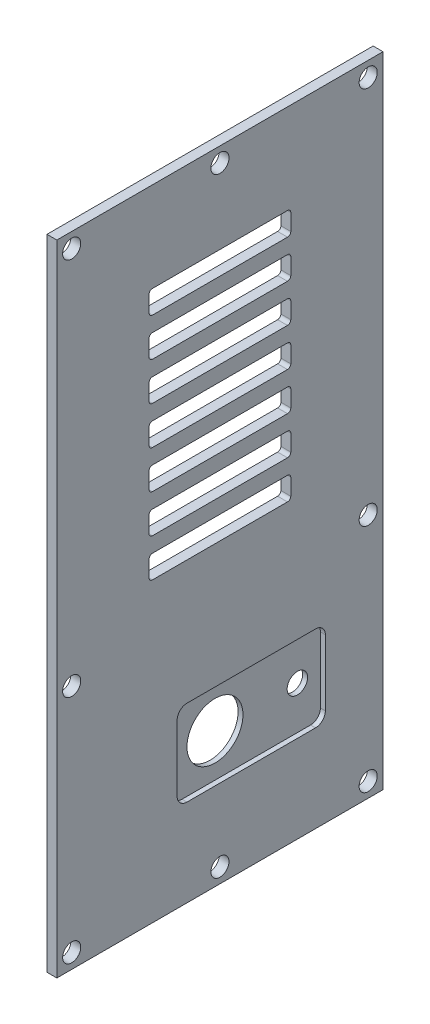
SolidWorks part; units mm, degrees
ref_plane "Front Plane" through (0, 0, 0) normal (0, 0, 1) x (1, 0, 0)
ref_plane "Top Plane" through (0, 0, 0) normal (0, 1, 0) x (1, 0, 0)
ref_plane "Right Plane" through (0, 0, 0) normal (1, 0, 0) x (0, 0, -1)
sketch "Sketch1" plane through (-74.9883, 0, 0) normal (-1, 0, 0) x (0, 0, 1)
  line L0 (-65.7307, 104.5) -> (-65.7307, -89.5)
  line L1 (-66.2307, 105) -> (33.7693, 105) construction
  line L2 (-66.2307, 105) -> (-66.2307, -90) construction
  line L3 (-66.2307, -90) -> (33.7693, -90) construction
  line L4 (33.7693, 105) -> (33.7693, -90) construction
  line L5 (-65.7307, -89.5) -> (33.2693, -89.5)
  line L6 (33.2693, 104.5) -> (33.2693, -89.5)
  line L7 (-65.7307, 104.5) -> (33.2693, 104.5)
  dimension "D1" = 0.5
extrude "Boss-Extrude1" add sketch "Sketch1" along normal blind 3
sketch "Sketch2" plane through (-77.9883, 0, 0) normal (-1, 0, 0) x (0, 0, 1)
  line L0 (-65.7307, 73.75) -> (33.2693, 73.75) construction
  line L1 (-65.7307, 104.5) -> (-65.7307, -89.5) construction
  line L2 (33.2693, -89.5) -> (33.2693, 104.5) construction
  line L3 (-16.2307, 104.5) -> (-16.2307, -89.5) construction
  line L4 (33.2693, 104.5) -> (-65.7307, 104.5) construction
  line L5 (-65.7307, -89.5) -> (33.2693, -89.5) construction
  line L6 (-65.7307, 62.15) -> (33.2693, 62.15) construction
  line L7 (33.2693, 50.55) -> (-65.7307, 50.55) construction
  line L8 (33.2693, 38.95) -> (-65.7307, 38.95) construction
  line L9 (-65.7307, 27.35) -> (33.2693, 27.35) construction
  line L10 (33.2693, 15.75) -> (-65.7307, 15.75) construction
  line L11 (33.2693, 4.15) -> (-65.7307, 4.15) construction
  line L13 (-37.7307, 70.25) -> (5.2693, 70.25)
  line L14 (-37.7307, 70.25) -> (-37.7307, 77.25)
  line L15 (-37.7307, 77.25) -> (5.2693, 77.25)
  line L16 (5.2693, 70.25) -> (5.2693, 77.25)
  line L17 (-37.7307, 70.25) -> (5.2693, 77.25) construction
  line L18 (-37.7307, 77.25) -> (5.2693, 70.25) construction
  line L19 (-37.7307, 58.65) -> (5.2693, 58.65)
  line L20 (-37.7307, 58.65) -> (-37.7307, 65.65)
  line L21 (-37.7307, 65.65) -> (5.2693, 65.65)
  line L22 (5.2693, 58.65) -> (5.2693, 65.65)
  line L23 (-37.7307, 58.65) -> (5.2693, 65.65) construction
  line L24 (-37.7307, 65.65) -> (5.2693, 58.65) construction
  line L25 (-37.7307, 47.05) -> (5.2693, 47.05)
  line L26 (-37.7307, 47.05) -> (-37.7307, 54.05)
  line L27 (-37.7307, 54.05) -> (5.2693, 54.05)
  line L28 (5.2693, 47.05) -> (5.2693, 54.05)
  line L29 (-37.7307, 47.05) -> (5.2693, 54.05) construction
  line L30 (-37.7307, 54.05) -> (5.2693, 47.05) construction
  line L31 (-37.7307, 35.45) -> (5.2693, 35.45)
  line L32 (-37.7307, 35.45) -> (-37.7307, 42.45)
  line L33 (-37.7307, 42.45) -> (5.2693, 42.45)
  line L34 (5.2693, 35.45) -> (5.2693, 42.45)
  line L35 (-37.7307, 35.45) -> (5.2693, 42.45) construction
  line L36 (-37.7307, 42.45) -> (5.2693, 35.45) construction
  line L37 (-37.7307, 23.85) -> (5.2693, 23.85)
  line L38 (-37.7307, 23.85) -> (-37.7307, 30.85)
  line L39 (-37.7307, 30.85) -> (5.2693, 30.85)
  line L40 (5.2693, 23.85) -> (5.2693, 30.85)
  line L41 (-37.7307, 23.85) -> (5.2693, 30.85) construction
  line L42 (-37.7307, 30.85) -> (5.2693, 23.85) construction
  line L43 (-37.7307, 12.25) -> (5.2693, 12.25)
  line L44 (-37.7307, 12.25) -> (-37.7307, 19.25)
  line L45 (-37.7307, 19.25) -> (5.2693, 19.25)
  line L46 (5.2693, 12.25) -> (5.2693, 19.25)
  line L47 (-37.7307, 12.25) -> (5.2693, 19.25) construction
  line L48 (-37.7307, 19.25) -> (5.2693, 12.25) construction
  line L49 (-37.7307, 0.65) -> (5.2693, 0.65)
  line L50 (-37.7307, 0.65) -> (-37.7307, 7.65)
  line L51 (-37.7307, 7.65) -> (5.2693, 7.65)
  line L52 (5.2693, 0.65) -> (5.2693, 7.65)
  line L53 (-37.7307, 0.65) -> (5.2693, 7.65) construction
  line L54 (-37.7307, 7.65) -> (5.2693, 0.65) construction
  point P24 (-16.2307, 73.75)
  point P25 (-16.2307, 62.15)
  point P26 (-16.2307, 50.55)
  point P27 (-16.2307, 38.95)
  point P28 (-16.2307, 27.35)
  point P29 (-16.2307, 15.75)
  point P30 (-16.2307, 4.15)
  point P31 (-16.2307, 73.75)
  point P36 (-16.2307, 62.15)
  point P41 (-16.2307, 50.55)
  point P46 (-16.2307, 38.95)
  point P51 (-16.2307, 27.35)
  point P56 (-16.2307, 15.75)
  point P61 (-16.2307, 4.15)
  dimension "D1" = 43
  dimension "D2" = 7
extrude "Cut-Extrude1" cut sketch "Sketch2" against normal through all
fillet "Fillet1" radius 1 28 edges at (-76.4883, 7.65, 5.2693) (-76.4883, 0.65, 5.2693) (-76.4883, 0.65, -37.7307) (-76.4883, 7.65, -37.7307) (-76.4883, 12.25, -37.7307) (-76.4883, 19.25, -37.7307) (-76.4883, 12.25, 5.2693) (-76.4883, 19.25, 5.2693) (-76.4883, 23.85, 5.2693) (-76.4883, 23.85, -37.7307) (-76.4883, 30.85, -37.7307) (-76.4883, 30.85, 5.2693) (-76.4883, 42.45, 5.2693) (-76.4883, 35.45, 5.2693) (-76.4883, 35.45, -37.7307) (-76.4883, 42.45, -37.7307) (-76.4883, 47.05, -37.7307) (-76.4883, 54.05, -37.7307) (-76.4883, 47.05, 5.2693) (-76.4883, 54.05, 5.2693) (-76.4883, 58.65, 5.2693) (-76.4883, 65.65, 5.2693) (-76.4883, 65.65, -37.7307) (-76.4883, 58.65, -37.7307) (-76.4883, 70.25, -37.7307) (-76.4883, 77.25, -37.7307) (-76.4883, 70.25, 5.2693) (-76.4883, 77.25, 5.2693)
sketch "Sketch3" plane through (-77.9883, 0, 0) normal (-1, 0, 0) x (0, 0, 1)
  line L1 (-65.7307, -89.5) -> (33.2693, -89.5) construction
  line L5 (-56.2307, -90) -> (-56.2307, 105) construction
  line L6 (33.2693, -89.5) -> (33.2693, 104.5) construction
  circle A0 centre (-16.2307, -50) radius 8.5
  circle A1 centre (-41.2307, -50) radius 3.1
  dimension "D3" = 6.2
  dimension "D4" = 17
  dimension "D1" = 39.5
  dimension "D2" = 39.5
  dimension "D5" = 49.5
  dimension "D6" = 15
extrude "Cut-Extrude2" cut sketch "Sketch3" against normal through all
sketch "Sketch4" plane through (-74.9883, 0, 0) normal (1, 0, 0) x (0, 0, -1)
  line L0 (65.7307, -89.5) -> (-33.2693, -89.5) construction
  line L1 (3.2307, -63) -> (48.2307, -63)
  line L2 (3.2307, -63) -> (3.2307, -37)
  line L3 (3.2307, -37) -> (48.2307, -37)
  line L4 (48.2307, -63) -> (48.2307, -37)
  line L5 (3.2307, -63) -> (48.2307, -37) construction
  line L6 (3.2307, -37) -> (48.2307, -63) construction
  line L7 (65.7307, 104.5) -> (65.7307, -89.5) construction
  circle A0 centre (16.2307, -50) radius 8.5 construction
  point P0 (25.7307, -50)
  dimension "D1" = 45
  dimension "D2" = 26
  dimension "D3" = 39.5
  dimension "D4" = 13
  dimension "D5" = 40
  dimension "D6" = 26.5
extrude "Cut-Extrude3" cut sketch "Sketch4" against normal blind 1.5
fillet "Fillet2" radius 3 4 edges at (-75.7383, -63, -48.2307) (-75.7383, -37, -48.2307) (-75.7383, -63, -3.2307) (-75.7383, -37, -3.2307)
sketch "Sketch5" plane through (-77.9883, 0, 0) normal (-1, 0, 0) x (0, 0, 1)
  line L0 (-65.7307, 104.5) -> (-65.7307, -89.5) construction
  line L1 (33.2693, 104.5) -> (-65.7307, 104.5) construction
  line L2 (-65.7307, -89.5) -> (33.2693, -89.5) construction
  line L3 (33.2693, -89.5) -> (33.2693, 104.5) construction
  circle A0 centre (-61.2307, 100) radius 2.75
  circle A1 centre (28.7693, 100) radius 2.75
  circle A2 centre (-61.2307, -15) radius 2.75
  circle A3 centre (-61.2307, -85) radius 2.75
  circle A4 centre (28.7693, -85) radius 2.75
  circle A5 centre (28.7693, -15) radius 2.75
  circle A6 centre (-16.2307, 100) radius 2.75
  circle A7 centre (-16.2307, -85) radius 2.75
  dimension "D1" = 5.5
  dimension "D7" = 45
  dimension "D8" = 5.5
  dimension "D9" = 5.5
  dimension "D2" = 4.5
  dimension "D3" = 4.5
  dimension "D4" = 4.5
  dimension "D5" = 4.5
  dimension "D6" = 70
extrude "Cut-Extrude4" cut sketch "Sketch5" against normal through all
